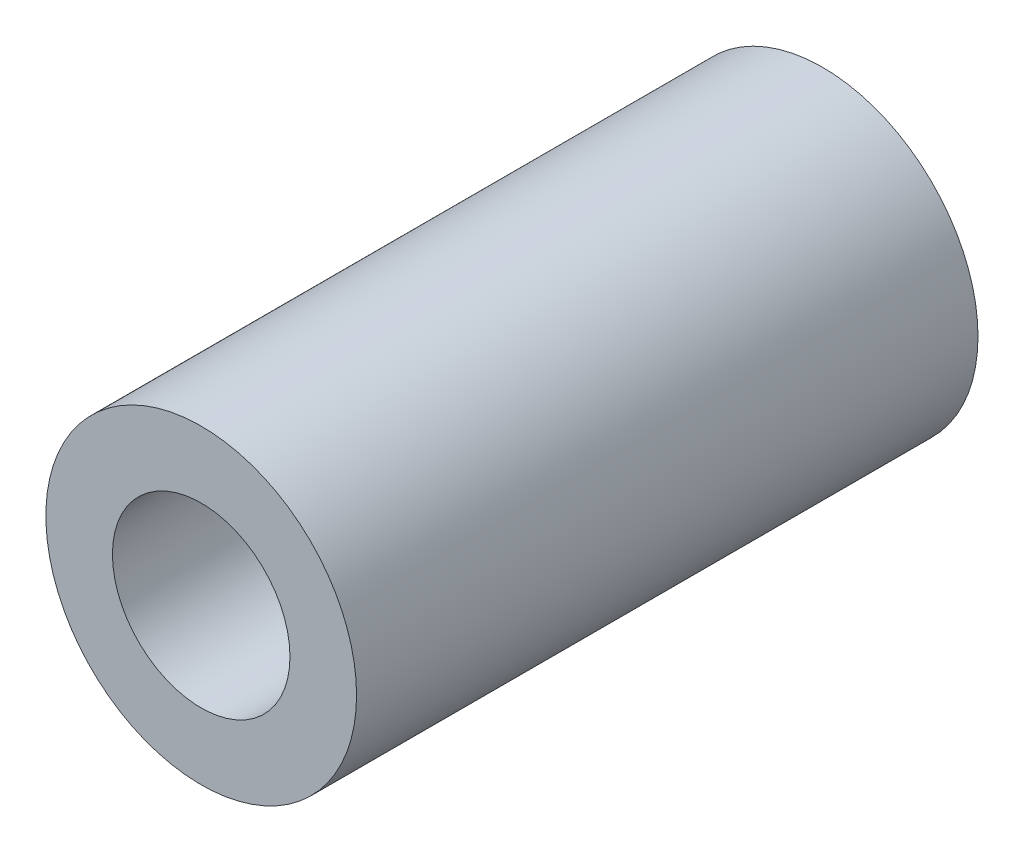
SolidWorks part; units mm, degrees
ref_plane "Front Plane" through (0, 0, 0) normal (0, 0, 1) x (1, 0, 0)
ref_plane "Top Plane" through (0, 0, 0) normal (0, 1, 0) x (1, 0, 0)
ref_plane "Right Plane" through (0, 0, 0) normal (1, 0, 0) x (0, 0, -1)
sketch "Sketch1" plane through (0, 0, 0) normal (0, 0, 1) x (1, 0, 0)
  circle A0 centre (0, 0) radius 7
  circle A1 centre (0, 0) radius 4
  dimension "D1" = 14
  dimension "D2" = 8
extrude "Boss-Extrude1" add sketch "Sketch1" along normal mid plane 28
